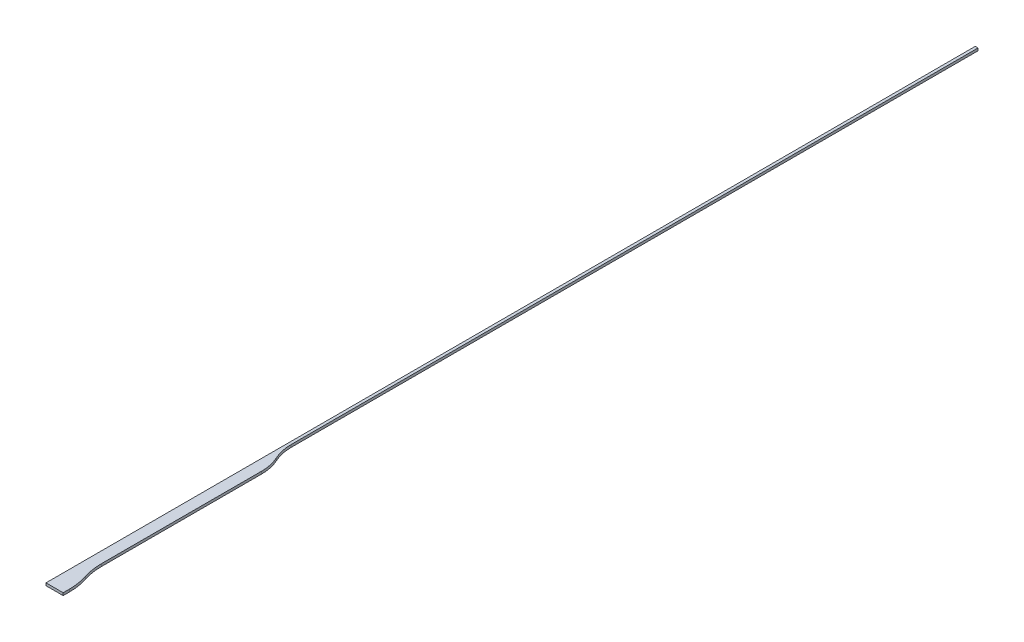
SolidWorks part; units mm, degrees
ref_plane "Front" through (0, 0, 0) normal (0, 0, 1) x (1, 0, 0)
ref_plane "Top" through (0, 0, 0) normal (0, 1, 0) x (1, 0, 0)
ref_plane "Right" through (0, 0, 0) normal (1, 0, 0) x (0, 0, -1)
sketch "Sketch1" plane through (0, 0, 0) normal (0, 1, 0) x (1, 0, 0)
  line L0 (-147, 0) -> (-147, 25)
  line L1 (0, 0) -> (-108.8862, 0) construction
  line L2 (-171, 175) -> (-171, 810.4)
  line L3 (-204, 960.4) -> (-204, 3680.9998)
  arc A0 (-204, 960.4) -> (-187.5, 885.4) centre (-25.2955, 960.4) ccw
  arc A1 (-171, 810.4) -> (-187.5, 885.4) centre (-349.7045, 810.4) ccw
  arc A2 (-147, 25) -> (-159, 100) centre (-387.375, 25) ccw
  arc A3 (-171, 175) -> (-159, 100) centre (69.375, 175) ccw
  dimension "D1" = 150
  dimension "D2" = 150
  dimension "D3" = 147
  dimension "D4" = 171
  dimension "D5" = 204
  dimension "D6" = 25
  dimension "D7" = 810.4
  dimension "D8" = 3680.9998
extrude "Extrude-Thin1" add sketch "Sketch1" along normal mid plane 10 thin thin type one direction reverse wall 11
sketch "Sketch3" plane through (0, 5, 0) normal (0, 1, 0) x (1, 0, 0)
  line L0 (-158, 0) -> (-158, 25) construction
  line L1 (-182, 175) -> (-182, 810.4) construction
  line L2 (-158, 0) -> (-158, 25)
  line L3 (-182, 175) -> (-182, 810.4)
  line L4 (-215, 960.4) -> (-215, 0)
  line L5 (-215, 960.4) -> (-215, 3680.9998) construction
  line L6 (-215, 0) -> (-158, 0)
  line L7 (-147, 0) -> (-158, 0) construction
  arc A0 (-158, 25) -> (-169.4509, 96.5679) centre (-387.375, 25) ccw construction
  arc A1 (-182, 175) -> (-169.4509, 96.5679) centre (69.375, 175) ccw construction
  arc A2 (-182, 810.4) -> (-197.4844, 880.7834) centre (-349.7045, 810.4) ccw construction
  arc A3 (-215, 960.4) -> (-197.4844, 880.7834) centre (-25.2955, 960.4) ccw construction
  arc A4 (-158, 25) -> (-169.4509, 96.5679) centre (-387.375, 25) ccw
  arc A5 (-182, 175) -> (-169.4509, 96.5679) centre (69.375, 175) ccw
  arc A6 (-182, 810.4) -> (-197.4844, 880.7834) centre (-349.7045, 810.4) ccw
  arc A7 (-215, 960.4) -> (-197.4844, 880.7834) centre (-25.2955, 960.4) ccw
extrude "Extrude1" add sketch "Sketch3" against normal up to surface (10 mm away) up to face at (-179.2631, -5, -829.1373)
fillet "Fillet1" [suppressed] radius 5
